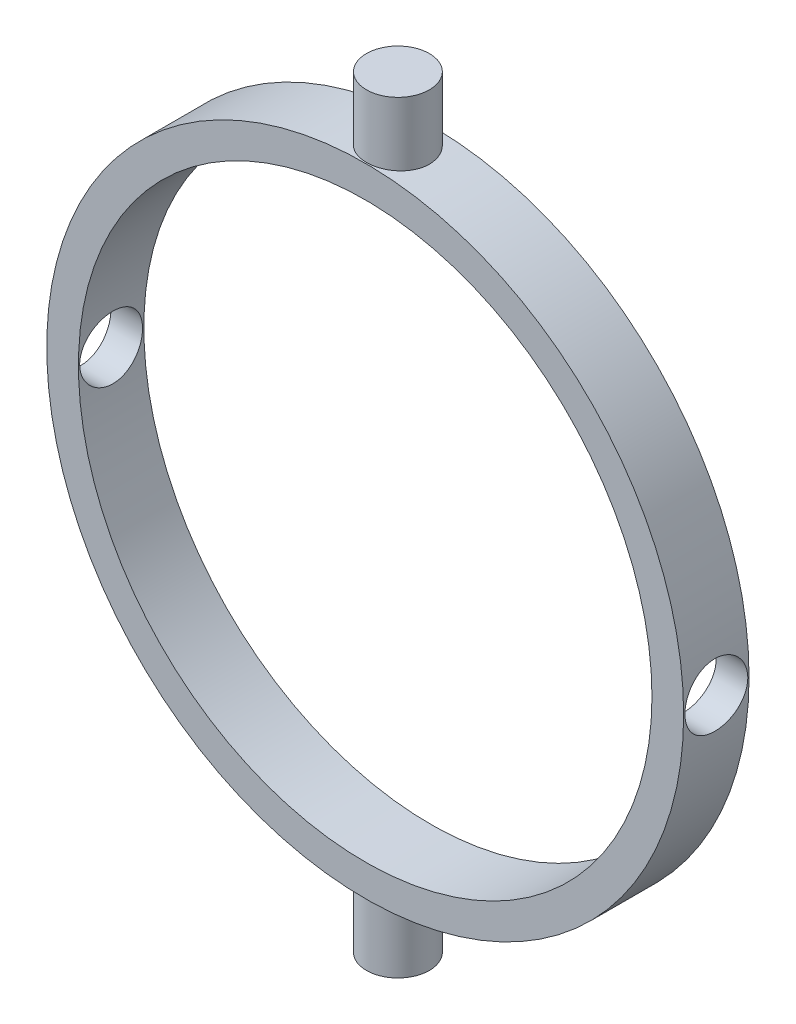
SolidWorks part; units mm, degrees
ref_plane "Front Plane" through (0, 0, 0) normal (0, 0, 1) x (1, 0, 0)
ref_plane "Top Plane" through (0, 0, 0) normal (0, 1, 0) x (1, 0, 0)
ref_plane "Right Plane" through (0, 0, 0) normal (1, 0, 0) x (0, 0, -1)
sketch "Sketch1" plane through (0, 0, 0) normal (0, 0, 1) x (1, 0, 0)
  circle A0 centre (0, 0) radius 14.478
  circle A1 centre (0, 0) radius 16.078
  dimension "D1" = 28.956
  dimension "D2" = 1.6
extrude "Boss-Extrude1" add sketch "Sketch1" along normal blind 3.302
ref_plane "Plane1" through (16.078, 0, 0) normal (1, 0, 0) x (0, 0, -1)
sketch "Sketch2" plane through (16.078, 0, 0) normal (1, 0, 0) x (0, 0, -1)
  line L0 (-1.651, 0) -> (0, 0) construction
  line L1 (0, 3.198) -> (-3.302, 3.198) construction
  line L2 (-3.302, 16.078) -> (-3.302, -16.078) construction
  line L3 (0, -16.078) -> (0, 16.078) construction
  line L4 (-1.651, 3.198) -> (-1.651, 0) construction
  circle A0 centre (-1.651, 0) radius 1.5875
  dimension "D1" = 3.175
extrude "Cut-Extrude1" cut sketch "Sketch2" against normal through all
ref_plane "Plane2" through (0, 16.078, 0) normal (0, 1, 0) x (-1, 0, 0)
sketch "Sketch3" plane through (0, 16.078, 0) normal (0, 1, 0) x (-1, 0, 0)
  line L0 (4.6335, 3.302) -> (4.6335, 0) construction
  line L1 (-16.078, 0) -> (16.078, 0) construction
  line L2 (16.078, 3.302) -> (-16.078, 3.302) construction
  line L3 (4.6335, 1.651) -> (0, 1.651) construction
  line L4 (0, 0) -> (0, 1.651) construction
  circle A0 centre (0, 1.651) radius 1.5875
  dimension "D1" = 3.175
extrude "Boss-Extrude2" add sketch "Sketch3" along normal blind 3.175 and the other way blind 0.635
pattern_circular "CirPattern1" count 2 over 360 about axis through (0, 0, 3.302) along (0, 0, -1) of "Boss-Extrude2"
